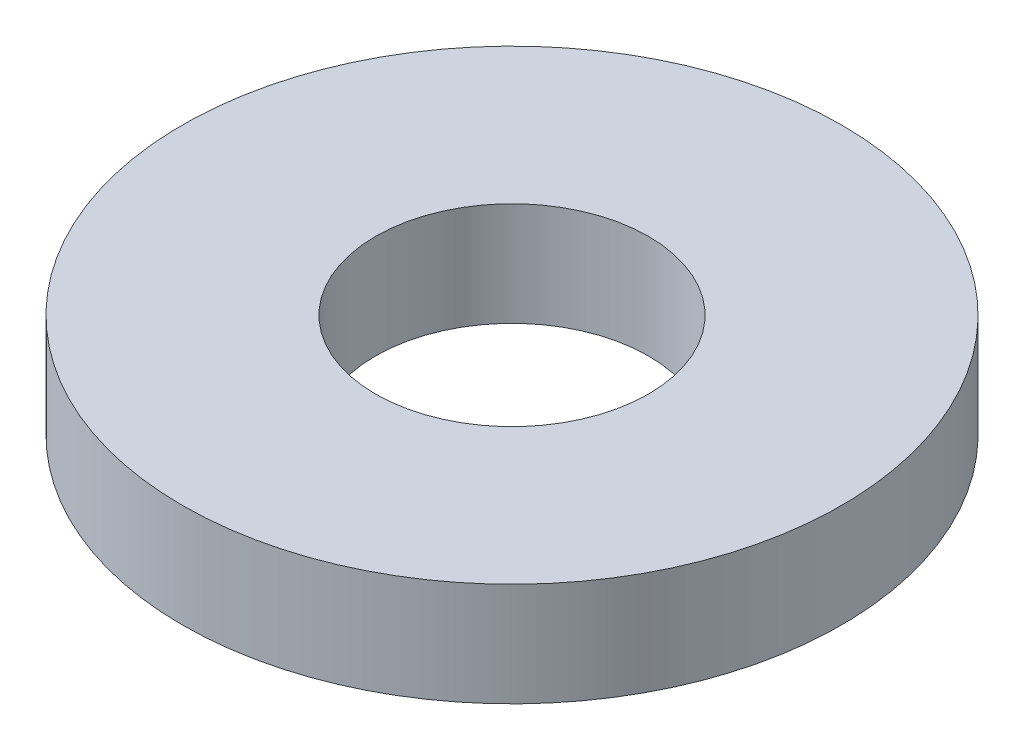
SolidWorks part; units mm, degrees
ref_plane "Front Plane" through (0, 0, 0) normal (0, 0, 1) x (1, 0, 0)
ref_plane "Top Plane" through (0, 0, 0) normal (0, 1, 0) x (1, 0, 0)
ref_plane "Right Plane" through (0, 0, 0) normal (1, 0, 0) x (0, 0, -1)
sketch "Sketch1" plane through (0, 0, 0) normal (0, 1, 0) x (1, 0, 0)
  circle A0 centre (0, 0) radius 3.5
  circle A1 centre (0, 0) radius 1.45
  dimension "D1" = 7
  dimension "D2" = 2.9
extrude "Boss-Extrude1" add sketch "Sketch1" along normal blind 1.1
